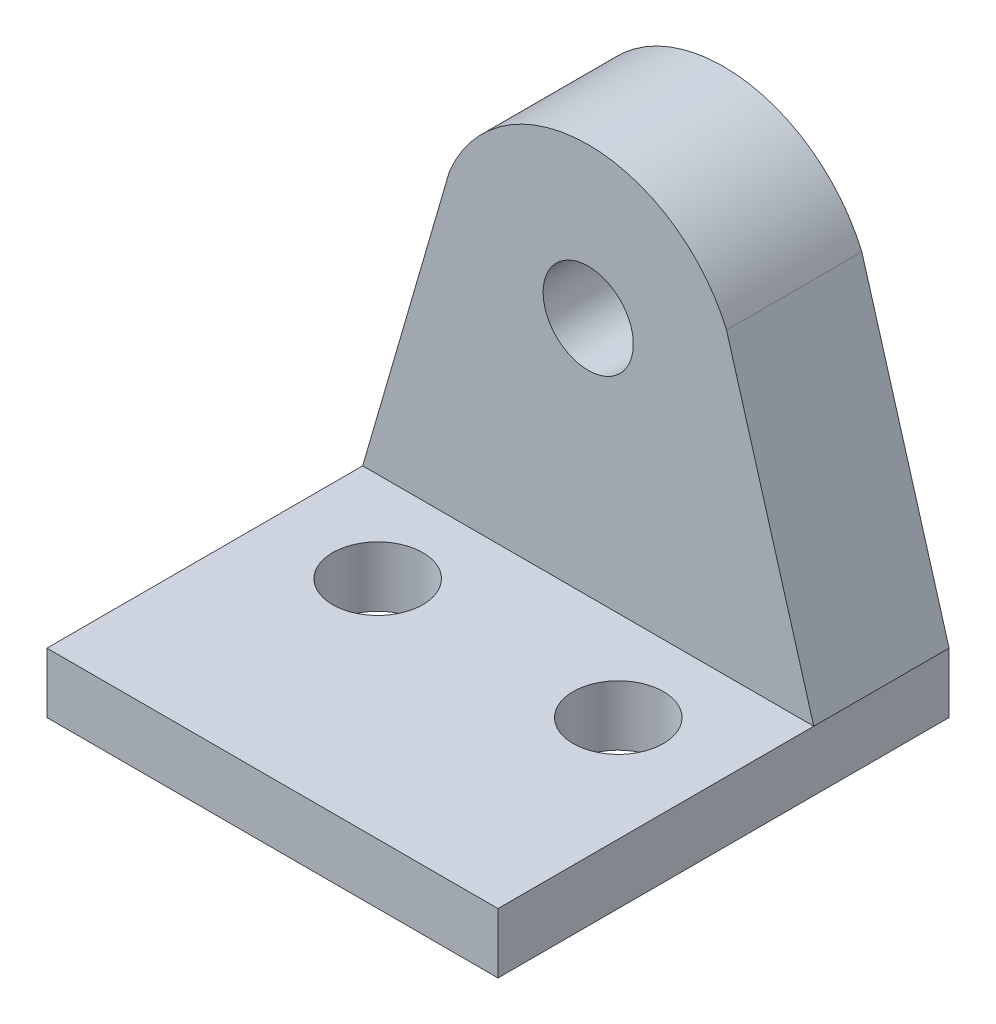
SolidWorks part; units mm, degrees
ref_plane "Front Plane" through (0, 0, 0) normal (0, 0, 1) x (1, 0, 0)
ref_plane "Top Plane" through (0, 0, 0) normal (0, 1, 0) x (1, 0, 0)
ref_plane "Right Plane" through (0, 0, 0) normal (1, 0, 0) x (0, 0, -1)
sketch "Sketch7" plane through (0, 0, 0) normal (0, 1, 0) x (1, 0, 0)
  line L0 (-7.5, 0) -> (7.5, 0)
  line L1 (7.5, 0) -> (7.5, -7.5)
  line L2 (7.5, -7.5) -> (-7.5, -7.5)
  line L3 (-7.5, -7.5) -> (-7.5, 0)
  point P4 (0, 0)
  dimension "D1" = 15
  dimension "D2" = 7.5
extrude "Boss-Extrude2" add sketch "Sketch7" along normal blind 2
sketch "Sketch8" plane through (0, 0, 0) normal (0, 0, -1) x (-1, 0, 0)
  line L0 (-4.599, 11.962) -> (-7.5, 2)
  line L1 (-7.5, 2) -> (7.5, 2) construction
  line L2 (4.615, 11.9239) -> (7.5, 2)
  line L3 (-7.5, 2) -> (7.5, 2)
  circle A0 centre (0, 10) radius 1.5
  arc A1 (-4.599, 11.962) -> (4.615, 11.9239) centre (0, 10) cw
extrude "Boss-Extrude3" add sketch "Sketch8" against normal blind 4.5
mirror "Mirror1" about plane through (7.5, 2, 7.5) normal (0, 0, -1) of "Boss-Extrude2"
sketch "Sketch9" plane through (0, 2, 0) normal (0, 1, 0) x (1, 0, 0)
  circle A0 centre (4, -7.5) radius 1.5
extrude "Cut-Extrude1" cut sketch "Sketch9" against normal through all
mirror "Mirror2" about plane through (0, 0, 0) normal (1, 0, 0) of "Cut-Extrude1"
